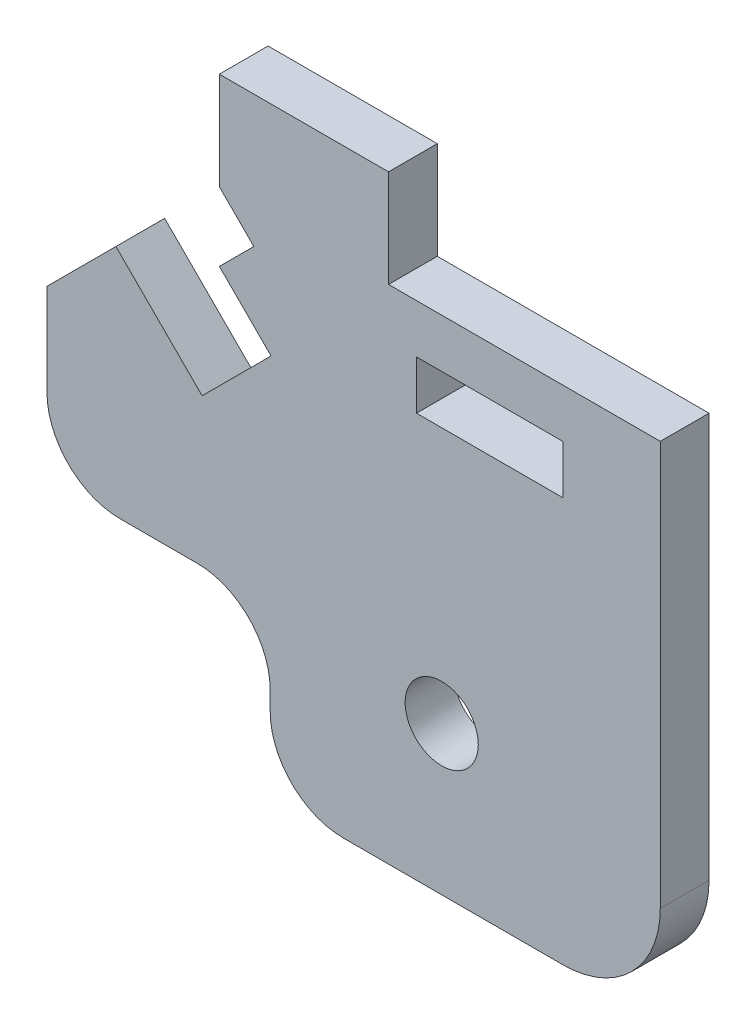
SolidWorks part; units mm, degrees
material "Acrylic (Medium-high impact)"
ref_plane "Front Plane" through (0, 0, 0) normal (0, 0, 1) x (1, 0, 0)
ref_plane "Top Plane" through (0, 0, 0) normal (0, 1, 0) x (1, 0, 0)
ref_plane "Right Plane" through (0, 0, 0) normal (1, 0, 0) x (0, 0, -1)
sketch "Model" plane through (0, 0, 0) normal (0, 0, 1) x (1, 0, 0)
  line L223 (6.364, 1.1716) -> (2.8284, 4.7071)
  line L224 (14.0104, 8.9497) -> (25.1569, 8.9497)
  line L225 (6.1569, -4.8787) -> (5.8284, -4.8787)
  line L226 (21.1569, -11.6414) -> (12.1569, -11.6414)
  line L227 (2.8284, 4.7071) -> (0, 1.8787)
  line L228 (3, -4.8787) -> (5.8284, -4.8787)
  line L229 (7.7782, 2.5858) -> (5.6569, 4.7071)
  line L230 (8.4853, 7.5355) -> (7.0711, 8.9497)
  line L231 (0, -1.8787) -> (0, 1.8787)
  line L232 (9.1569, -8.6414) -> (9.1569, -7.8787)
  line L233 (25.1569, 8.9497) -> (25.1569, -7.6414)
  line L234 (7.0711, 12.9497) -> (14.0104, 12.9497)
  line L235 (21.1569, 4.9497) -> (21.1569, 6.9497)
  line L236 (21.1569, 4.9497) -> (15.1569, 4.9497)
  line L237 (15.1569, 4.9497) -> (15.1569, 6.9497)
  line L238 (15.1569, 6.9497) -> (21.1569, 6.9497)
  line L255 (5.6569, 4.7071) -> (8.4853, 7.5355)
  line L256 (7.0711, 8.9497) -> (7.0711, 12.9497)
  line L257 (6.364, 1.1716) -> (7.7782, 2.5858)
  line L364 (14.0104, 8.9497) -> (14.0104, 12.9497)
  circle A99 centre (16.1917, -5.5589) radius 1.5
  arc A100 (21.1569, -11.6414) -> (25.1569, -7.6414) centre (21.1569, -7.6414) ccw
  arc A101 (9.1569, -8.6414) -> (12.1569, -11.6414) centre (12.1569, -8.6414) ccw
  arc A102 (9.1569, -7.8787) -> (6.1569, -4.8787) centre (6.1569, -7.8787) ccw
  arc A103 (0, -1.8787) -> (3, -4.8787) centre (3, -1.8787) ccw
  dimension "D1" = 3
  dimension "D2" = 4
  dimension "D3" = 3
  dimension "D4" = 5.6569
  dimension "D5" = 5.8284
  dimension "D6" = 6.364
  dimension "D7" = 9.1569
  dimension "D8" = 14.0104
  dimension "D9" = 16.1917
  dimension "D10" = 25.1569
  dimension "D11" = 1.1716
  dimension "D12" = 4.9497
  dimension "D20" = 4.8787
  dimension "D21" = 5.5589
  dimension "D22" = 11.6414
extrude "Boss-Extrude1" add sketch "Model" along normal blind 2
sketch "Sketch7" plane through (0, 0, 2) normal (0, 0, 1) x (1, 0, 0)
  line L0 (3.0711, 12.9497) -> (7.0711, 8.9497)
  line L1 (7.0711, 12.9497) -> (3.0711, 12.9497)
surface "Surface-Fill1" [suppressed]
sketch "Sketch10" [suppressed] plane through (0, 0, 2) normal (0, 0, 1) x (1, 0, 0)
  line L3 (7.0711, 12.9497) -> (3.0711, 12.9497)
  line L4 (7.0711, 8.9497) -> (7.0711, 12.9497)
  line L5 (3.0711, 12.9497) -> (7.0711, 8.9497)
  line L6 (7.0711, 12.9497) -> (3.0711, 12.9497)
  line L7 (7.0711, 8.9497) -> (7.0711, 12.9497)
  line L8 (3.0711, 12.9497) -> (7.0711, 8.9497)
  dimension "D1" = 0
extrude "Boss-Extrude2" [suppressed] add sketch "Sketch10" against normal blind 2
sketch "Sketch15" plane through (5.182, 5.182, 0) normal (-0.7071, -0.7071, 0) x (0, 0, 1)
  line L1 (0, -3.6716) -> (2, -3.6716)
  line L2 (0, -3.6716) -> (0, -0.6716)
  line L3 (0, -0.6716) -> (2, -0.6716)
  line L4 (2, -3.6716) -> (2, -0.6716)
extrude "Cut-Extrude1" cut sketch "Sketch15" against normal blind 2
